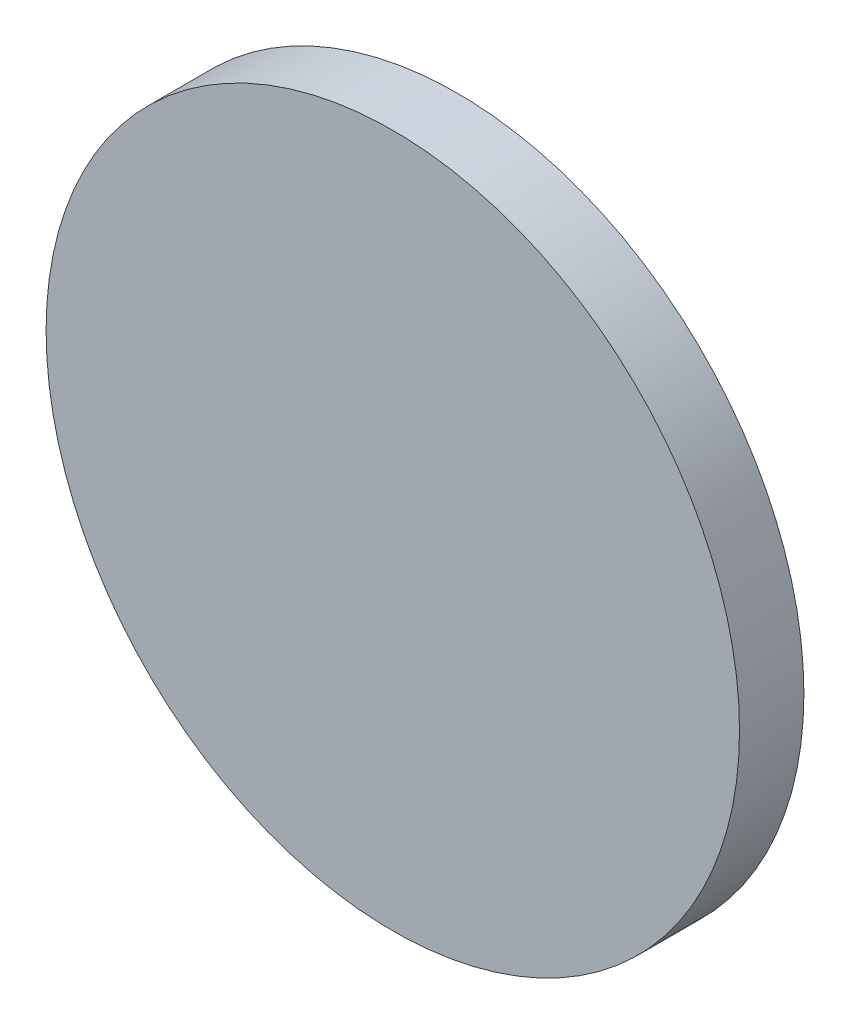
SolidWorks part; units mm, degrees
ref_plane "Ebene vorne" through (0, 0, 0) normal (0, 0, 1) x (1, 0, 0)
ref_plane "Ebene oben" through (0, 0, 0) normal (0, 1, 0) x (1, 0, 0)
ref_plane "Ebene rechts" through (0, 0, 0) normal (1, 0, 0) x (0, 0, -1)
sketch "Skizze1" plane through (0, 0, 0) normal (0, 0, 1) x (1, 0, 0)
  circle A0 centre (0, 0) radius 35
  dimension "D1" = 70
extrude "Aufsatz-Linear austragen1" add sketch "Skizze1" along normal blind 6.5
